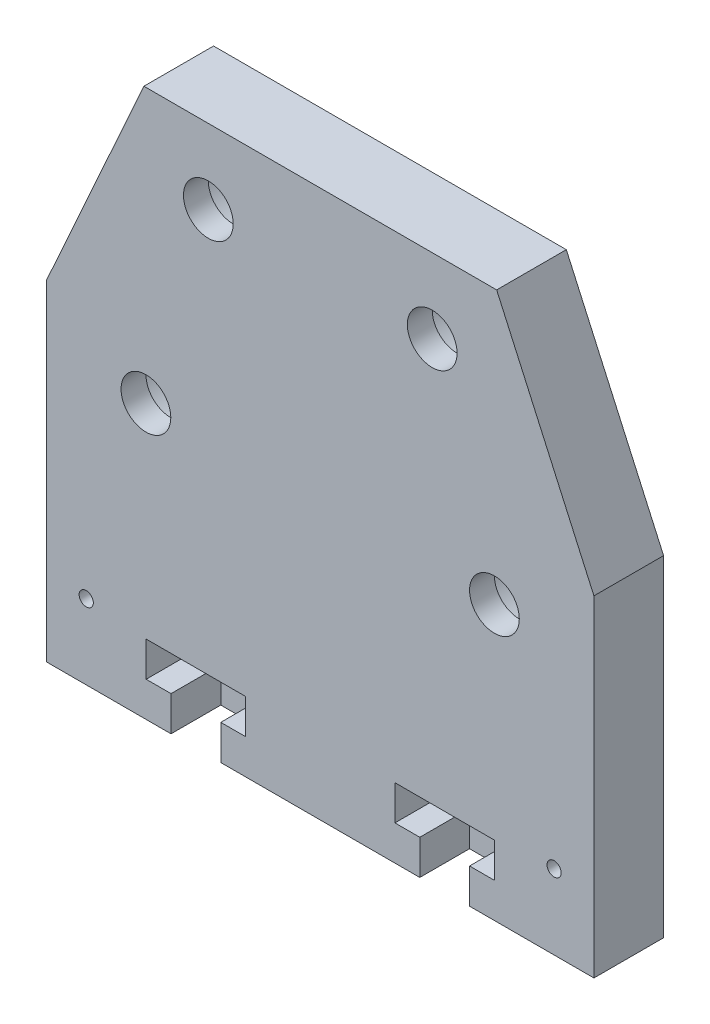
SolidWorks part; units mm, degrees
ref_plane "Front Plane" through (0, 0, 0) normal (0, 0, 1) x (1, 0, 0)
ref_plane "Top Plane" through (0, 0, 0) normal (0, 1, 0) x (1, 0, 0)
ref_plane "Right Plane" through (0, 0, 0) normal (1, 0, 0) x (0, 0, -1)
sketch "Sketch3" plane through (0, 0, 0) normal (0, 0, 1) x (1, 0, 0)
  line L0 (33.7824, 5.0217) -> (14.1872, -38.5696)
  line L1 (104.6814, 5.0217) -> (33.7824, 5.0217)
  line L3 (124.2289, -104.9783) -> (14.1872, -104.9783)
  line L5 (114.4868, -16.7913) -> (14.1872, -90.317) construction
  line L6 (124.2289, -90.3112) -> (23.977, -16.7913) construction
  line L7 (104.6814, 5.0217) -> (124.2289, -38.4636)
  line L8 (14.1872, -38.5696) -> (14.1872, -104.9783)
  line L9 (124.2289, -38.4636) -> (124.2289, -104.9783)
  circle A0 centre (91.7289, -9.9783) radius 11.05
  circle A1 centre (46.7289, -9.9783) radius 11.05
  circle A2 centre (104.2289, -49.9783) radius 11.05
  circle A3 centre (34.1872, -49.9783) radius 11.05
  point P0 (69.2229, -49.9725)
  dimension "D7" = 22.1
  dimension "D8" = 22.1
  dimension "D13" = 22.1
  dimension "D14" = 22.1
  dimension "D2" = 20
  dimension "D3" = 15
  dimension "D4" = 15
  dimension "D5" = 45
  dimension "D9" = 55
  dimension "D11" = 55
  dimension "D15" = 20
extrude "Boss-Extrude1" add sketch "Sketch3" along normal blind 14
sketch "Sketch4" plane through (0, 0, 14) normal (0, 0, 1) x (1, 0, 0)
  circle A0 centre (91.7289, -9.9783) radius 5
  circle A1 centre (46.7289, -9.9783) radius 5
  circle A2 centre (104.2289, -49.9783) radius 5
  circle A3 centre (34.1872, -49.9783) radius 5
  circle A4 centre (34.1872, -49.9783) radius 11.05 construction
  circle A5 centre (46.7289, -9.9783) radius 11.05 construction
  circle A6 centre (91.7289, -9.9783) radius 11.05 construction
  circle A7 centre (104.2289, -49.9783) radius 11.05 construction
  circle A8 centre (46.7289, -9.9783) radius 11.05
  circle A9 centre (91.7289, -9.9783) radius 11.05
  circle A10 centre (104.2289, -49.9783) radius 11.05
  circle A11 centre (34.1872, -49.9783) radius 11.05
  dimension "D6" = 22.1
  dimension "D8" = 22.1
  dimension "D10" = 22.1
  dimension "D12" = 22.1
  dimension "D13" = 10
  dimension "D14" = 10
  dimension "D15" = 10
  dimension "D16" = 10
  dimension "D1" = 0
  dimension "D2" = 0
  dimension "D3" = 0
  dimension "D4" = 0
  dimension "D5" = 0
  dimension "D7" = 0
  dimension "D9" = 0
  dimension "D11" = 0
sketch "Sketch5" plane through (0, 0, 14) normal (0, 0, 1) x (1, 0, 0)
  line L1 (39.2319, -97.9783) -> (49.2319, -97.9783)
  line L2 (39.2319, -97.9783) -> (39.2319, -104.9783)
  line L3 (39.2319, -104.9783) -> (49.2319, -104.9783)
  line L4 (49.2319, -97.9783) -> (49.2319, -104.9783)
  line L5 (34.2319, -90.9783) -> (54.2319, -90.9783)
  line L6 (34.2319, -90.9783) -> (34.2319, -97.9783)
  line L7 (34.2319, -97.9783) -> (54.2319, -97.9783)
  line L8 (54.2319, -90.9783) -> (54.2319, -97.9783)
  line L9 (89.2319, -97.9783) -> (99.2319, -97.9783)
  line L10 (89.2319, -97.9783) -> (89.2319, -104.9783)
  line L11 (89.2319, -104.9783) -> (99.2319, -104.9783)
  line L12 (99.2319, -97.9783) -> (99.2319, -104.9783)
  line L13 (84.2319, -90.9783) -> (104.2319, -90.9783)
  line L14 (84.2319, -90.9783) -> (84.2319, -97.9783)
  line L15 (84.2319, -97.9783) -> (104.2319, -97.9783)
  line L16 (104.2319, -90.9783) -> (104.2319, -97.9783)
  line L17 (14.1872, -104.9783) -> (124.2289, -104.9783) construction
  line M4 (14.1872, -104.9783) -> (124.2289, -104.9783)
  dimension "D3" = 0
  dimension "D4" = 7
  dimension "D5" = 0
  dimension "D6" = 7
  dimension "D7" = 20
  dimension "D8" = 0
  dimension "D9" = 7
  dimension "D10" = 0
  dimension "D11" = 7
  dimension "D14" = 10
  dimension "D15" = 20
  dimension "D16" = 10
extrude "Cut-Extrude3" cut sketch "Sketch5" against normal blind 10 contours L8 L5 L6 L7 L1 | L4 L1 L2 M4 | L16 L13 L14 L15 L9 | L12 L9 L10 M4
sketch "Sketch6" plane through (0, 0, 14) normal (0, 0, 1) x (1, 0, 0)
  circle A0 centre (46.7289, -9.9783) radius 11.05
  circle A1 centre (46.7289, -9.9783) radius 6
  circle A2 centre (91.7289, -9.9783) radius 11.05
  circle A3 centre (91.7289, -9.9783) radius 6
  circle A4 centre (34.1872, -49.9783) radius 11.05
  circle A5 centre (34.1872, -49.9783) radius 6
  circle A6 centre (104.2289, -49.9783) radius 11.05
  circle A7 centre (104.2289, -49.9783) radius 6
  circle A8 centre (46.7289, -9.9783) radius 11.05 construction
  circle A9 centre (91.7289, -9.9783) radius 11.05 construction
  circle A10 centre (34.1872, -49.9783) radius 11.05 construction
  circle A11 centre (104.2289, -49.9783) radius 11.05 construction
  dimension "D1" = 0
  dimension "D2" = 0
  dimension "D3" = 22.1
  dimension "D4" = 12
  dimension "D5" = 0
  dimension "D6" = 0
  dimension "D7" = 22.1
  dimension "D8" = 12
  dimension "D9" = 0
  dimension "D10" = 0
  dimension "D11" = 22.1
  dimension "D12" = 12
  dimension "D13" = 0
  dimension "D14" = 0
  dimension "D15" = 22.1
  dimension "D16" = 12
extrude "Boss-Extrude4" add sketch "Sketch6" against normal blind 5
sketch "Sketch7" plane through (0, 0, 14) normal (0, 0, 1) x (1, 0, 0)
  line L0 (14.1872, -104.9783) -> (39.2319, -104.9783) construction
  line L1 (14.1872, -38.5696) -> (14.1872, -104.9783) construction
  line L2 (99.2319, -104.9783) -> (124.2289, -104.9783) construction
  line L3 (124.2289, -104.9783) -> (124.2289, -38.4636) construction
  circle A0 centre (22.1872, -89.9783) radius 1.425
  circle A1 centre (116.2289, -89.9783) radius 1.425
  dimension "D1" = 2.85
  dimension "D6" = 2.85
  dimension "D2" = 15
  dimension "D3" = 8
  dimension "D4" = 15
  dimension "D5" = 8
sketch "Sketch8" plane through (0, 0, 14) normal (0, 0, 1) x (1, 0, 0)
  line L0 (14.1872, -104.9783) -> (39.2319, -104.9783) construction
  line L1 (99.2319, -104.9783) -> (124.2289, -104.9783) construction
  line L2 (124.2289, -104.9783) -> (124.2289, -38.4636) construction
  line L3 (14.1872, -38.5696) -> (14.1872, -104.9783) construction
  circle A0 centre (22.1872, -89.9783) radius 1.425
  circle A1 centre (116.2289, -89.9783) radius 1.425
  dimension "D5" = 2.85
  dimension "D6" = 2.85
  dimension "D1" = 15
  dimension "D2" = 15
  dimension "D3" = 8
  dimension "D4" = 8
extrude "Cut-Extrude5" cut sketch "Sketch8" against normal blind 14
extrude "Boss-Extrude2" add sketch "Sketch4" against normal blind 5
